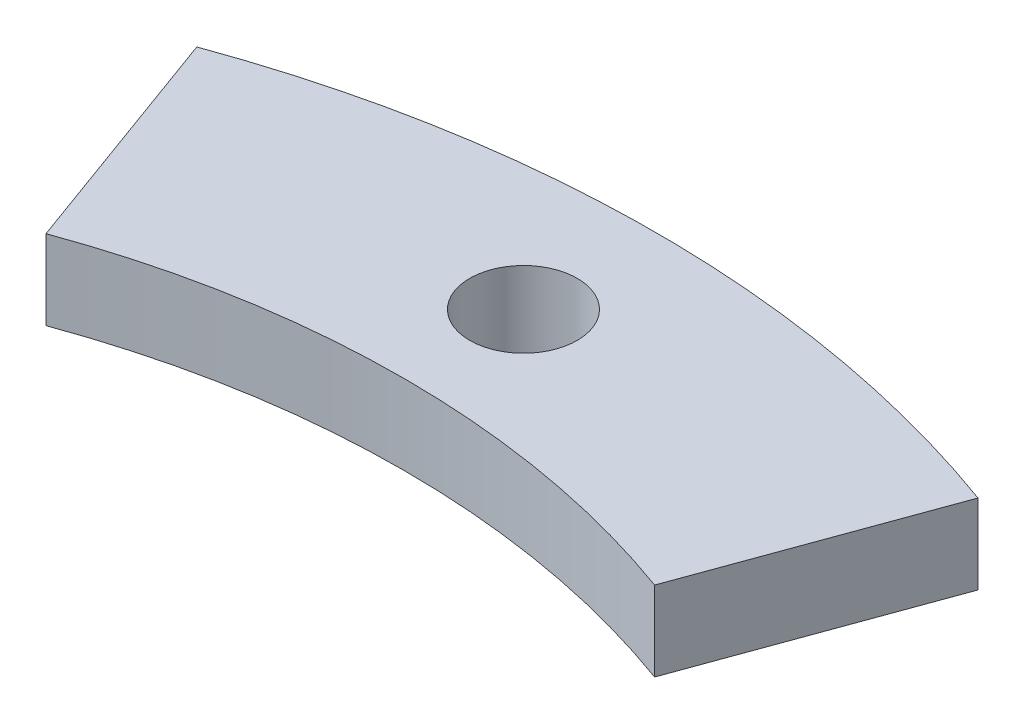
SolidWorks part; units mm, degrees
ref_plane "Front Plane" through (0, 0, 0) normal (0, 0, 1) x (1, 0, 0)
ref_plane "Top Plane" through (0, 0, 0) normal (0, 1, 0) x (1, 0, 0)
ref_plane "Right Plane" through (0, 0, 0) normal (1, 0, 0) x (0, 0, -1)
sketch "Sketch1" plane through (0, 0, 0) normal (0, 1, 0) x (1, 0, 0)
  circle A0 centre (0, 0) radius 38 construction
  circle A1 centre (0, 0) radius 43
  circle A2 centre (0, 0) radius 33.5
  dimension "D1" = 76
  dimension "D2" = 86
  dimension "D3" = 67
extrude "Boss-Extrude1" add sketch "Sketch1" along normal blind 3
sketch "Sketch2" plane through (0, 3, 0) normal (0, 1, 0) x (1, 0, 0)
  line L0 (0, 0) -> (0, -52.3198)
  line L1 (0, 0) -> (17.8944, 49.1646)
  arc A0 (17.8944, 49.1646) -> (0, -52.3198) centre (0, 0) cw
  dimension "D1" = 160
extrude "Cut-Extrude1" cut sketch "Sketch2" against normal through all both and the other way through all
mirror "Mirror1" about plane through (0, 0, 0) normal (1, 0, 0) of "Cut-Extrude1"
sketch "Sketch3" plane through (0, 3, 0) normal (0, 1, 0) x (1, 0, 0)
  line L0 (0, 0) -> (0, 43) construction
  arc A0 (14.7069, 40.4068) -> (-14.7069, 40.4068) centre (0, 0) ccw construction
  circle A1 centre (0, 38) radius 2.025
  dimension "D1" = 4.05
  dimension "D2" = 38
extrude "Cut-Extrude2" cut sketch "Sketch3" against normal through all both and the other way through all
